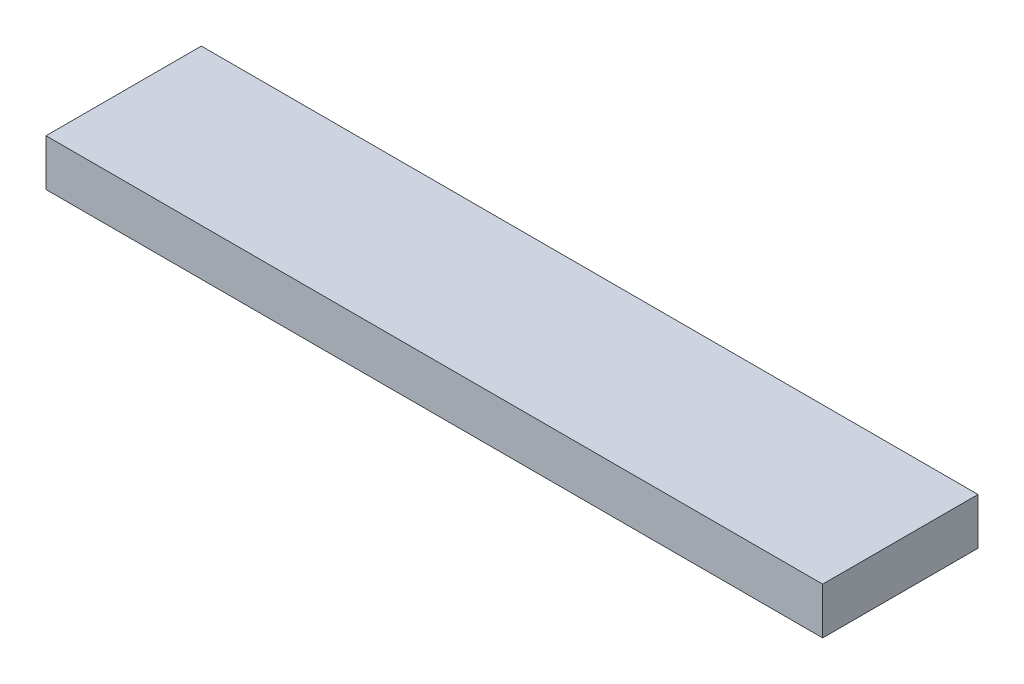
SolidWorks part; units mm, degrees
ref_plane "Front Plane" through (0, 0, 0) normal (0, 0, 1) x (1, 0, 0)
ref_plane "Top Plane" through (0, 0, 0) normal (0, 1, 0) x (1, 0, 0)
ref_plane "Right Plane" through (0, 0, 0) normal (1, 0, 0) x (0, 0, -1)
sketch "Sketch1" plane through (0, 0, 0) normal (0, 1, 0) x (1, 0, 0)
  line L1 (-64.1921, 23.508) -> (35.8079, 23.508)
  line L2 (-64.1921, 23.508) -> (-64.1921, 3.508)
  line L3 (-64.1921, 3.508) -> (35.8079, 3.508)
  line L4 (35.8079, 23.508) -> (35.8079, 3.508)
  dimension "D1" = 100
  dimension "D2" = 20
extrude "Boss-Extrude1" add sketch "Sketch1" along normal blind 6 contours L1 L4 L3 L2
